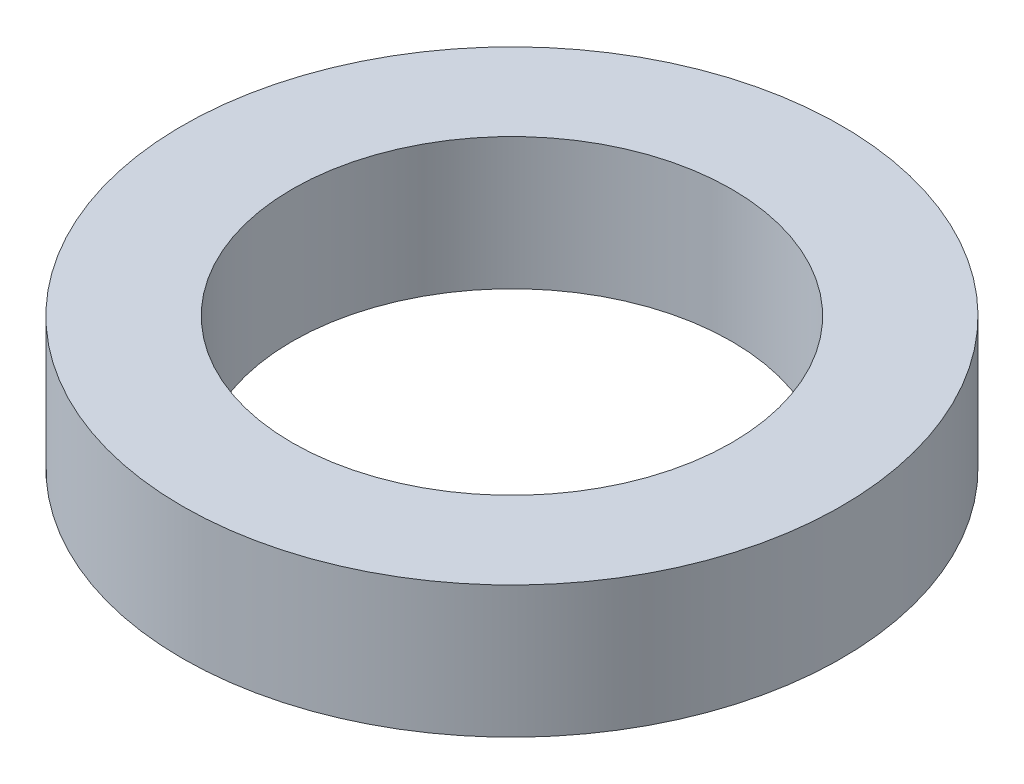
SolidWorks part; units mm, degrees
ref_plane "Front Plane" through (0, 0, 0) normal (0, 0, 1) x (1, 0, 0)
ref_plane "Top Plane" through (0, 0, 0) normal (0, 1, 0) x (1, 0, 0)
ref_plane "Right Plane" through (0, 0, 0) normal (1, 0, 0) x (0, 0, -1)
sketch "Sketch1" plane through (0, 0, 0) normal (0, 1, 0) x (1, 0, 0)
  circle A0 centre (0, 0) radius 5
  circle A1 centre (0, 0) radius 7.5
  dimension "D1" = 10
  dimension "D2" = 15
extrude "Boss-Extrude1" add sketch "Sketch1" along normal blind 3
